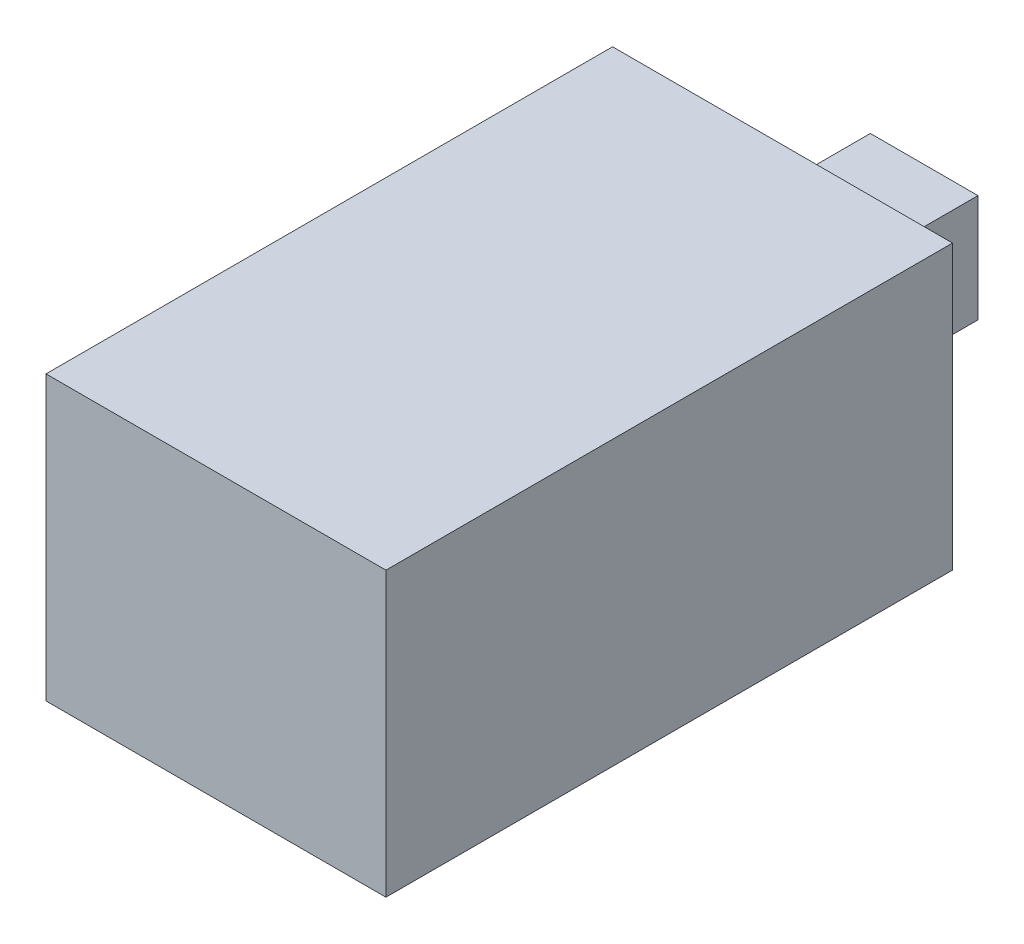
SolidWorks part; units mm, degrees
ref_plane "Front Plane" through (0, 0, 0) normal (0, 0, 1) x (1, 0, 0)
ref_plane "Top Plane" through (0, 0, 0) normal (0, 1, 0) x (1, 0, 0)
ref_plane "Right Plane" through (0, 0, 0) normal (1, 0, 0) x (0, 0, -1)
sketch "Sketch1" plane through (0, 0, 0) normal (0, 0, 1) x (1, 0, 0)
  line L1 (-6, -5) -> (6, -5)
  line L2 (-6, -5) -> (-6, 5)
  line L3 (-6, 5) -> (6, 5)
  line L4 (6, -5) -> (6, 5)
  line L5 (-6, -5) -> (6, 5) construction
  line L6 (-6, 5) -> (6, -5) construction
  point P0 (0, 0)
  dimension "D1" = 12
  dimension "D2" = 10
extrude "Boss-Extrude1" add sketch "Sketch1" along normal blind 20
sketch "Sketch2" plane through (0, 0, 0) normal (0, 0, -1) x (-1, 0, 0)
  line L1 (1.9, -1.9) -> (-1.9, -1.9)
  line L2 (1.9, -1.9) -> (1.9, 1.9)
  line L3 (1.9, 1.9) -> (-1.9, 1.9)
  line L4 (-1.9, -1.9) -> (-1.9, 1.9)
  line L5 (1.9, -1.9) -> (-1.9, 1.9) construction
  line L6 (1.9, 1.9) -> (-1.9, -1.9) construction
  point P0 (0, 0)
  dimension "D1" = 3.8
  dimension "D2" = 3.8
extrude "Boss-Extrude2" add sketch "Sketch2" along normal blind 5
